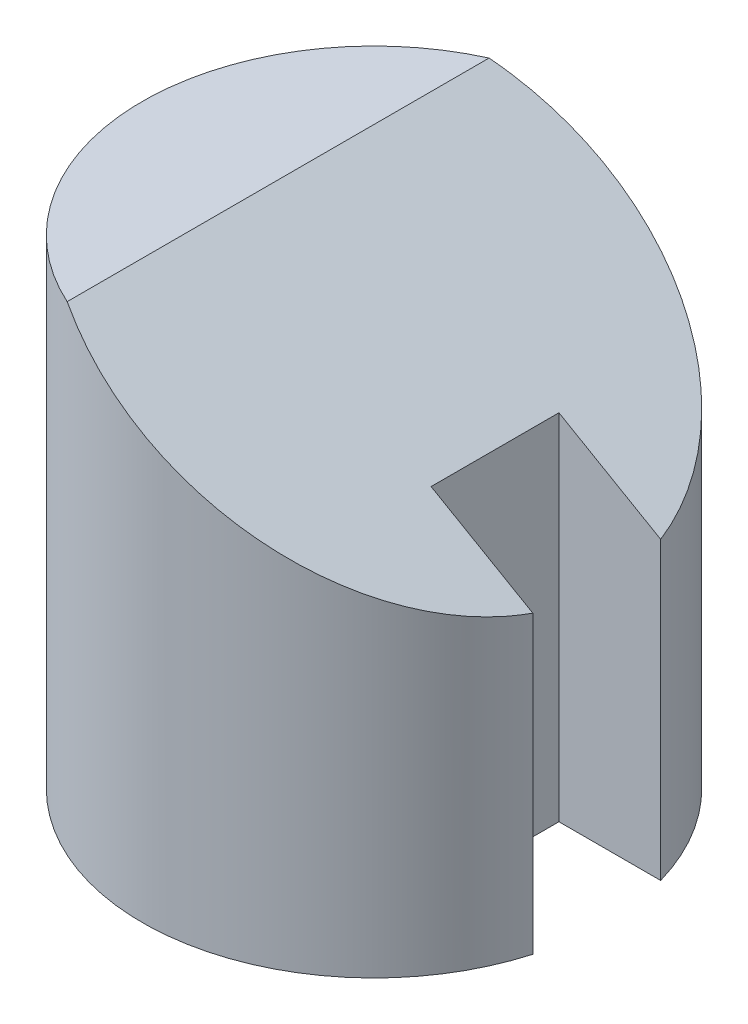
SolidWorks part; units mm, degrees
ref_plane "Front Plane" through (0, 0, 0) normal (0, 0, 1) x (1, 0, 0)
ref_plane "Top Plane" through (0, 0, 0) normal (0, 1, 0) x (1, 0, 0)
ref_plane "Right Plane" through (0, 0, 0) normal (1, 0, 0) x (0, 0, -1)
sketch "Sketch1" plane through (0, 0, 0) normal (0, 1, 0) x (1, 0, 0)
  circle A0 centre (0, 0) radius 29
  dimension "D1" = 58
extrude "Boss-Extrude1" add sketch "Sketch1" along normal blind 60
sketch "Sketch2" plane through (0, 0, 0) normal (0, 0, 1) x (1, 0, 0)
  line L0 (0, 61.6922) -> (0, -1.6365) construction
  line L1 (-12, 60) -> (29, 36.3286)
  line L2 (29, 60) -> (-29, 60) construction
  line L3 (29, 0) -> (29, 60) construction
  line L4 (29, 36.3286) -> (29, 60)
  line L5 (29, 60) -> (-12, 60)
  dimension "D1" = 12
  dimension "D2" = 30
extrude "Cut-Extrude1" cut sketch "Sketch2" along normal through all both and the other way through all
sketch "Sketch7" plane through (22.9808, 39.8038, 0) normal (0.5, 0.866, 0) x (0.866, -0.5, 0)
  line L0 (-58.2966, 0) -> (28.7578, 0) construction
  line L1 (5.6511, 8) -> (-9.0496, 8)
  line L2 (-9.0496, 8) -> (-9.0496, -8)
  line L3 (5.6511, -8) -> (-9.0496, -8)
  arc A0 (5.6511, 8) -> (5.6511, -8) centre (-18.3267, 0) cw
  ellipse E0 centre (-26.5359, 0) end of major axis (6.9504, 0) minor radius 29 (-40.3923, -26.4008) -> (-40.3923, 26.4008) ccw construction
  point P14 (-9.0496, 0)
  point P16 (5.6511, 8)
  dimension "D1" = 8
  dimension "D2" = 16
extrude "Cut-Extrude2" cut sketch "Sketch7" along direction (0, 1, 0) on the side against the normal through all
